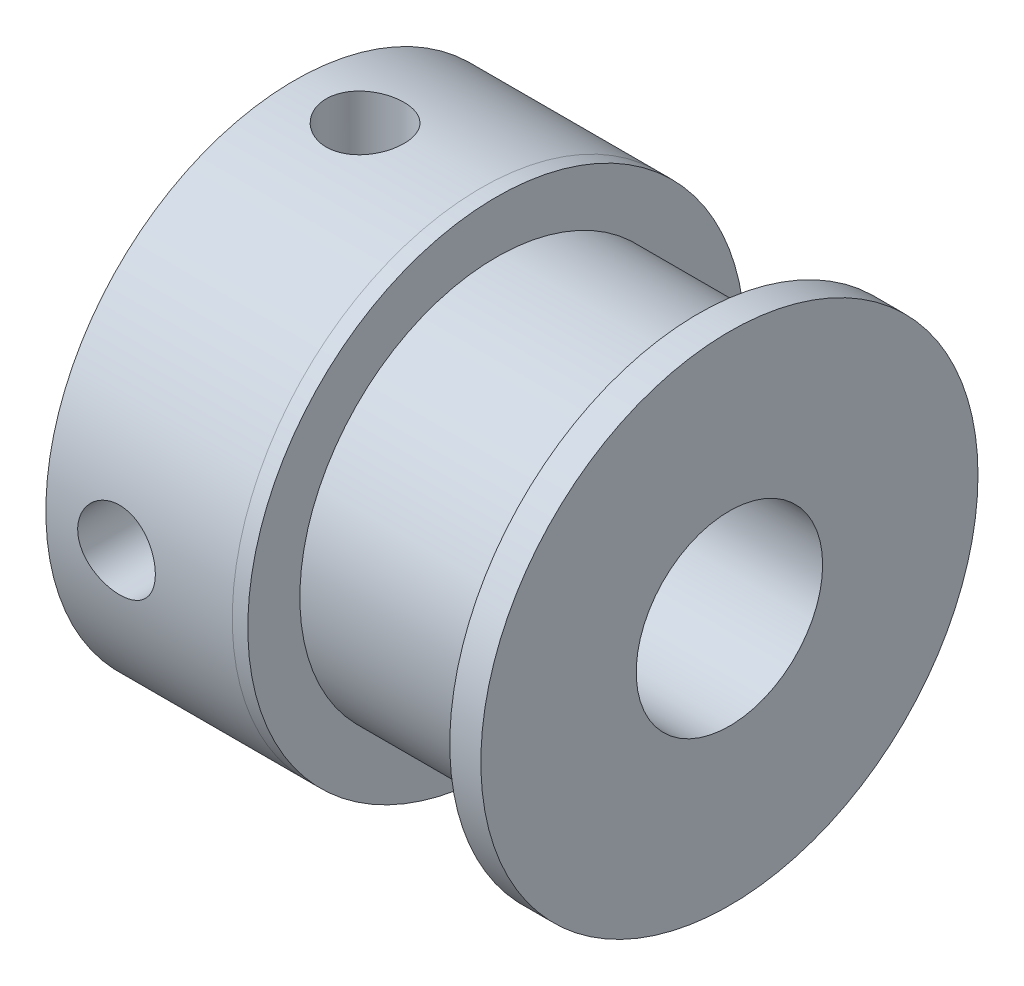
SolidWorks part; units mm, degrees
material "6061-T6 (SS)"
ref_plane "Front Plane" through (0, 0, 0) normal (0, 0, 1) x (1, 0, 0)
ref_plane "Top Plane" through (0, 0, 0) normal (0, 1, 0) x (1, 0, 0)
ref_plane "Right Plane" through (0, 0, 0) normal (1, 0, 0) x (0, 0, -1)
sketch "Sketch1" plane through (0, 0, 0) normal (0, 0, 1) x (1, 0, 0)
  line L0 (1.4515, 3) -> (1.4515, 7.9998)
  line L1 (7.4515, 8) -> (7.9515, 8)
  line L2 (7.9515, 8) -> (7.9515, 6.325)
  line L3 (7.9515, 6.325) -> (14.4515, 6.325)
  line L4 (14.4515, 6.325) -> (14.4515, 8)
  line L5 (14.4515, 8) -> (15.4515, 8)
  line L6 (15.4515, 8) -> (15.4515, 3)
  line L7 (15.4515, 3) -> (1.4515, 3)
  line L8 (0, 0) -> (-7.6744, 0) construction
  line L9 (7.4515, 8) -> (7.4515, 7.9998)
  line L10 (7.4515, 7.9998) -> (1.4515, 7.9998)
  dimension "D1" = 5
  dimension "D2" = 6.5
  dimension "D5" = 14
  dimension "D6" = 1
revolve "Revolve1" add sketch "Sketch1" angle 360 about L8
hole_wizard "M3x0.5 Tapped Hole1" positions "Sketch3" profile "Sketch2" tap size "M3x0.5" standard "ANSI Metric"
sketch "Sketch3" plane through (0, 0, 0) normal (0, 1, 0) x (1, 0, 0)
  line L0 (0, 0) -> (7.4515, 0) construction
  line L2 (7.4515, 7.9998) -> (7.4515, -7.9998) construction
  point P8 (3.7257, 0)
sketch "Sketch2" plane through (3.7257, 0, 0) normal (1, 0, 0) x (0, 0, -1)
  line L0 (0, 0) -> (0, 8)
  line L1 (0, 8) -> (1.25, 8)
  line L2 (1.25, 8) -> (1.25, 0)
  line L5 (1.25, 0) -> (0, 0)
  line L11 (0, -6.35) -> (0, 107.95) construction
  dimension "Thread Major Dia." = 2.5
  dimension "Thru Tap Drill Depth" = 8
hole_wizard "M3x0.5 Tapped Hole2" positions "Sketch5" profile "Sketch4" tap size "M3x0.5" standard "ANSI Metric"
sketch "Sketch5" plane through (0, 0, 0) normal (0, 0, 1) x (1, 0, 0)
  line L0 (0, 0) -> (7.4515, 0) construction
  line L2 (7.4515, 8) -> (7.4515, -8) construction
  point P7 (3.7257, 0)
sketch "Sketch4" plane through (3.7257, 0, 0) normal (1, 0, 0) x (0, 1, 0)
  line L0 (0, 0) -> (0, 8)
  line L1 (0, 8) -> (1.25, 8)
  line L2 (1.25, 8) -> (1.25, 0)
  line L5 (1.25, 0) -> (0, 0)
  line L11 (0, -6.35) -> (0, 107.95) construction
  dimension "Thread Major Dia." = 2.5
  dimension "Thru Tap Drill Depth" = 8
